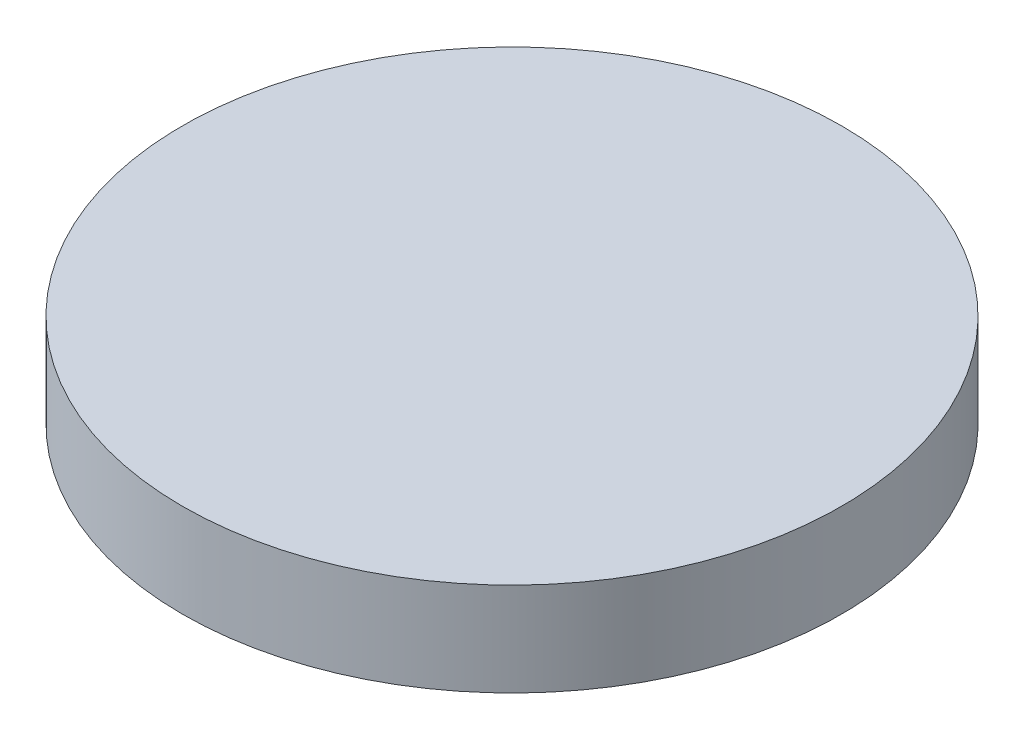
SolidWorks part; units mm, degrees
ref_plane "Front Plane" through (0, 0, 0) normal (0, 0, 1) x (1, 0, 0)
ref_plane "Top Plane" through (0, 0, 0) normal (0, 1, 0) x (1, 0, 0)
ref_plane "Right Plane" through (0, 0, 0) normal (1, 0, 0) x (0, 0, -1)
sketch "Sketch1" plane through (0, 0, 0) normal (0, 1, 0) x (1, 0, 0)
  circle A0 centre (0, 0) radius 1950
  dimension "D1" = 3900
extrude "Boss-Extrude1" add sketch "Sketch1" along normal mid plane 553
